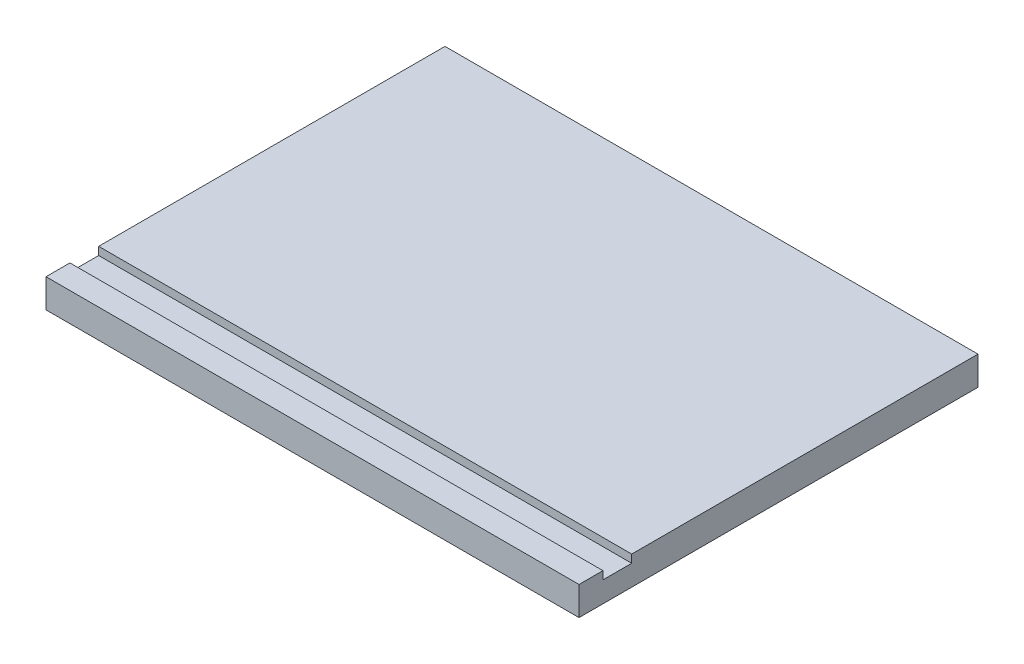
SolidWorks part; units mm, degrees
ref_plane "Спереди" through (0, 0, 0) normal (0, 0, 1) x (1, 0, 0)
ref_plane "Сверху" through (0, 0, 0) normal (0, 1, 0) x (1, 0, 0)
ref_plane "Справа" through (0, 0, 0) normal (1, 0, 0) x (0, 0, -1)
sketch "Эскиз1" plane through (0, 0, 0) normal (0, 1, 0) x (1, 0, 0)
  line L1 (167, -125) -> (-167, -125)
  line L2 (167, -125) -> (167, 125)
  line L3 (167, 125) -> (-167, 125)
  line L4 (-167, -125) -> (-167, 125)
  line L5 (167, -125) -> (-167, 125) construction
  line L6 (167, 125) -> (-167, -125) construction
  point P0 (0, 0)
  dimension "D1" = 334
  dimension "D2" = 250
extrude "Бобышка-Вытянуть1" add sketch "Эскиз1" along normal blind 18
sketch "Эскиз2" plane through (0, 18, 0) normal (0, 1, 0) x (1, 0, 0)
  line L0 (-167, 125) -> (-167, -125) construction
  line L1 (-167, -110) -> (167, -110)
  line L2 (-167, -110) -> (-167, -92)
  line L3 (-167, -92) -> (167, -92)
  line L4 (167, -110) -> (167, -92)
  line L5 (167, -125) -> (167, 125) construction
  line L6 (-167, -125) -> (167, -125) construction
  dimension "D1" = 15
  dimension "D2" = 18
extrude "Вырез-Вытянуть1" cut sketch "Эскиз2" against normal blind 5
